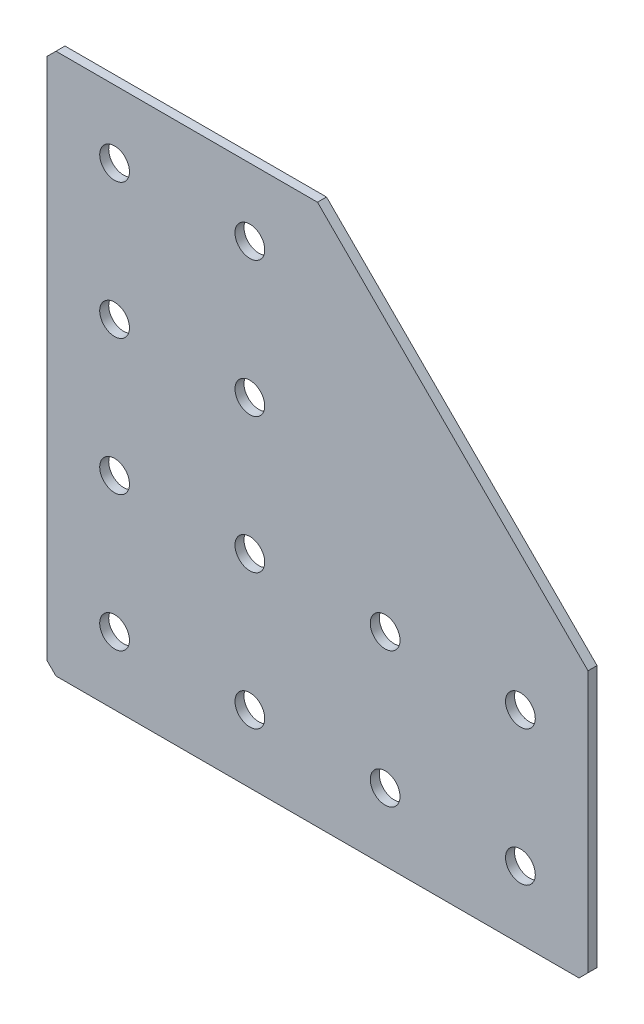
SolidWorks part; units mm, degrees
material "Простая углеродистая сталь"
ref_plane "Спереди(Плоскость XY)" through (0, 0, 0) normal (0, 0, 1) x (1, 0, 0)
ref_plane "Сверху(Плоскость XZ)" through (0, 0, 0) normal (0, 1, 0) x (1, 0, 0)
ref_plane "Справа(Плоскость ZY)" through (0, 0, 0) normal (1, 0, 0) x (0, 0, -1)
sketch "Эскиз1" plane through (0, 0, 0) normal (0, 0, -1) x (1, 0, 0)
  line L0 (0, 0) -> (0, 120)
  line L1 (0, 120) -> (120, 120)
  line L2 (120, 120) -> (120, 60)
  line L3 (120, 60) -> (60, 60) construction
  line L4 (60, 60) -> (60, 0) construction
  line L5 (60, 0) -> (0, 0)
  line L6 (120, 60) -> (60, 0)
  dimension "D1" = 120
  dimension "D2" = 60
  dimension "D3" = 60
  dimension "D4" = 120
extrude "Бобышка-Вытянуть1" add sketch "Эскиз1" along normal blind 2
hole_wizard "Отверстие с зазором M61" positions "Эскиз2" profile "Эскиз3" hole size "M6" standard "DIN" end condition through all
sketch "Эскиз2" plane through (0, 0, -2) normal (0, 0, -1) x (1, 0, 0)
  line L0 (15, 0) -> (15, 120) construction
  line L1 (0, 0) -> (60, 0) construction
  line L2 (120, 120) -> (0, 120) construction
  line L3 (0, 120) -> (0, 0) construction
  line L4 (0, 0) -> (60, 0) construction
  point P0 (15, 105)
  point P2 (15, 75)
  point P4 (15, 45)
  point P6 (15, 15)
  point P27 (45, 105)
  point P29 (45, 75)
  point P35 (45, 45)
  point P37 (45, 15)
  point P39 (75, 105)
  point P41 (75, 75)
  point P53 (105, 105)
  point P55 (105, 75)
  dimension "D1" = 30
  dimension "D2" = 30
  dimension "D3" = 30
  dimension "D4" = 15
  dimension "D5" = 30
  dimension "D6" = 15
  dimension "D7" = 30
  dimension "D8" = 30
sketch "Эскиз3" plane through (15, -105, -2) normal (1, 0, 0) x (0, 1, 0)
  line L0 (0, 0) -> (0, 2)
  line L1 (0, 2) -> (3.3, 2)
  line L2 (3.3, 2) -> (3.3, 0)
  line L5 (3.3, 0) -> (0, 0)
  line L11 (0, -6.35) -> (0, 107.95) construction
  dimension "Диаметр сквозного отверстия" = 6.6
  dimension "Глубина сквозного отверстия" = 2
chamfer "Фаска1" distance 2 angle 45 3 edges at (0, 0, -1) (120, -120, -1) (0, -120, -1)
